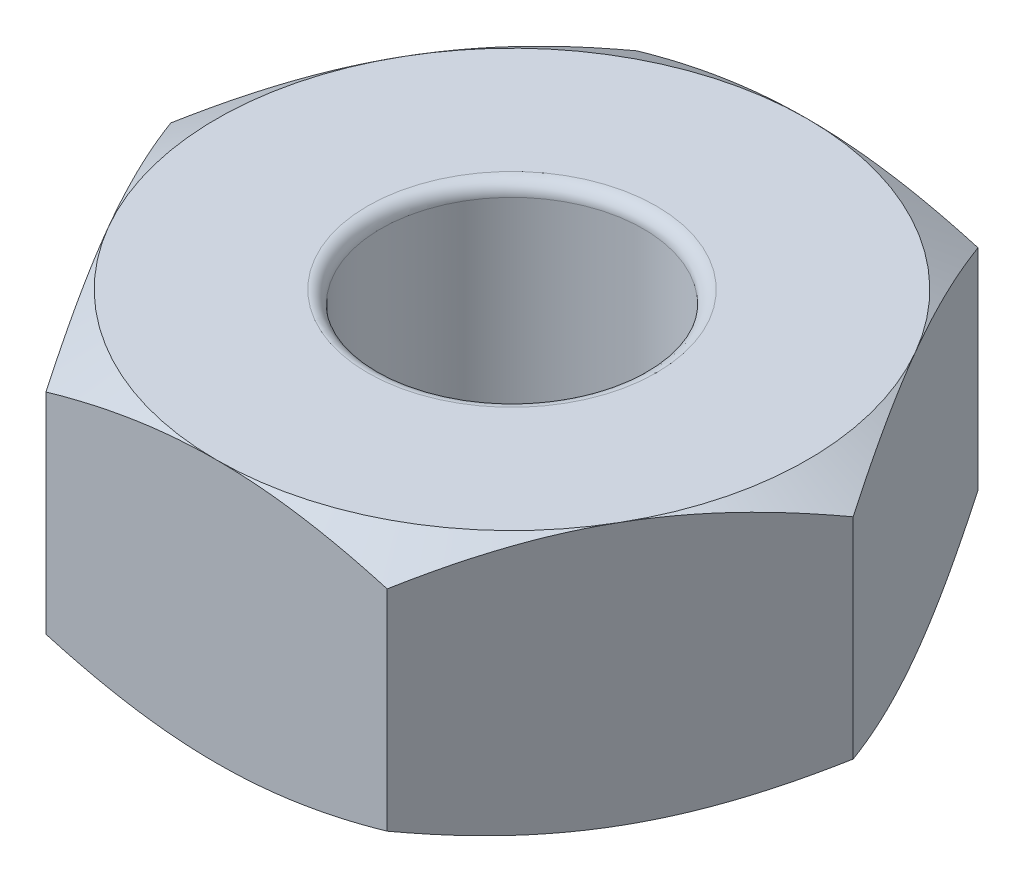
SolidWorks part; units mm, degrees
ref_plane "Front Plane" through (0, 0, 0) normal (0, 0, 1) x (1, 0, 0)
ref_plane "Top Plane" through (0, 0, 0) normal (0, 1, 0) x (1, 0, 0)
ref_plane "Right Plane" through (0, 0, 0) normal (1, 0, 0) x (0, 0, -1)
sketch "Sketch1" plane through (0, 0, 0) normal (0, 1, 0) x (1, 0, 0)
  line L1 (2.5981, 0) -> (1.299, 2.25)
  line L2 (1.299, 2.25) -> (-1.299, 2.25)
  line L3 (-1.299, 2.25) -> (-2.5981, 0)
  line L4 (-2.5981, 0) -> (-1.299, -2.25)
  line L5 (-1.299, -2.25) -> (1.299, -2.25)
  line L6 (1.299, -2.25) -> (2.5981, 0)
  circle A0 centre (0, 0) radius 2.25 construction
  circle A1 centre (0, 0) radius 1
  dimension "D1" = 2
  dimension "D2" = 4.5
extrude "Boss-Extrude1" add sketch "Sketch1" along normal blind 2
sketch "Sketch2" plane through (0, 0, 0) normal (0, 1, 0) x (1, 0, 0)
  circle A0 centre (0, 0) radius 2.25 construction
  circle A1 centre (0, 0) radius 2.25
extrude "Cut-Extrude2" cut sketch "Sketch2" along normal blind 2 draft 60 flip side to cut
sketch "Sketch3" plane through (0, 2, 0) normal (0, 1, 0) x (1, 0, 0)
  circle A0 centre (0, 0) radius 2.25 construction
  circle A1 centre (0, 0) radius 2.25
extrude "Cut-Extrude3" cut sketch "Sketch3" against normal blind 2 draft 60 flip side to cut
fillet "Fillet2" radius 0.1 2 edges at (0, 0, 1) (0, 2, 1)
